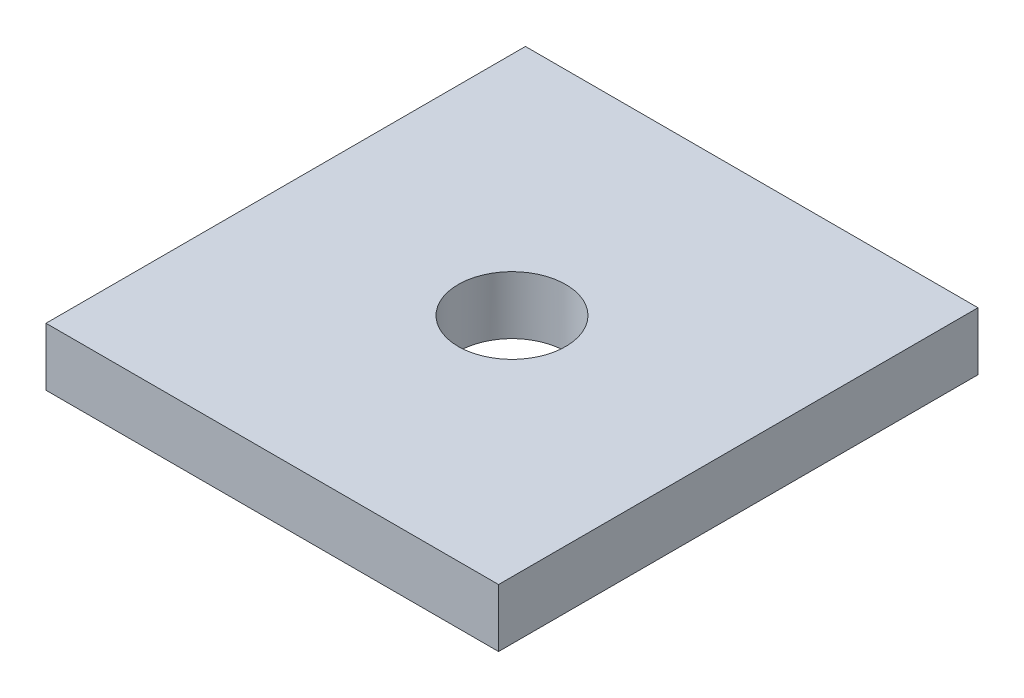
SolidWorks part; units mm, degrees
material "6061 Alloy"
ref_plane "Front Plane" through (0, 0, 0) normal (0, 0, 1) x (1, 0, 0)
ref_plane "Top Plane" through (0, 0, 0) normal (0, 1, 0) x (1, 0, 0)
ref_plane "Right Plane" through (0, 0, 0) normal (1, 0, 0) x (0, 0, -1)
sketch "Sketch1" plane through (0, 0, 0) normal (0, 1, 0) x (1, 0, 0)
  line L1 (-26.7335, -28.321) -> (26.7335, -28.321)
  line L2 (-26.7335, -28.321) -> (-26.7335, 28.321)
  line L3 (-26.7335, 28.321) -> (26.7335, 28.321)
  line L4 (26.7335, -28.321) -> (26.7335, 28.321)
  line L5 (-26.7335, -28.321) -> (26.7335, 28.321) construction
  line L6 (-26.7335, 28.321) -> (26.7335, -28.321) construction
  point P0 (0, 0)
  dimension "D1" = 56.642
  dimension "D2" = 53.467
extrude "Boss-Extrude2" add sketch "Sketch1" along normal blind 6.858
sketch "Sketch2" plane through (0, 6.858, 0) normal (0, 1, 0) x (1, 0, 0)
  circle A0 centre (0, 0) radius 6.35
  dimension "D1" = 12.7
extrude "Cut-Extrude1" cut sketch "Sketch2" against normal blind 25.4
